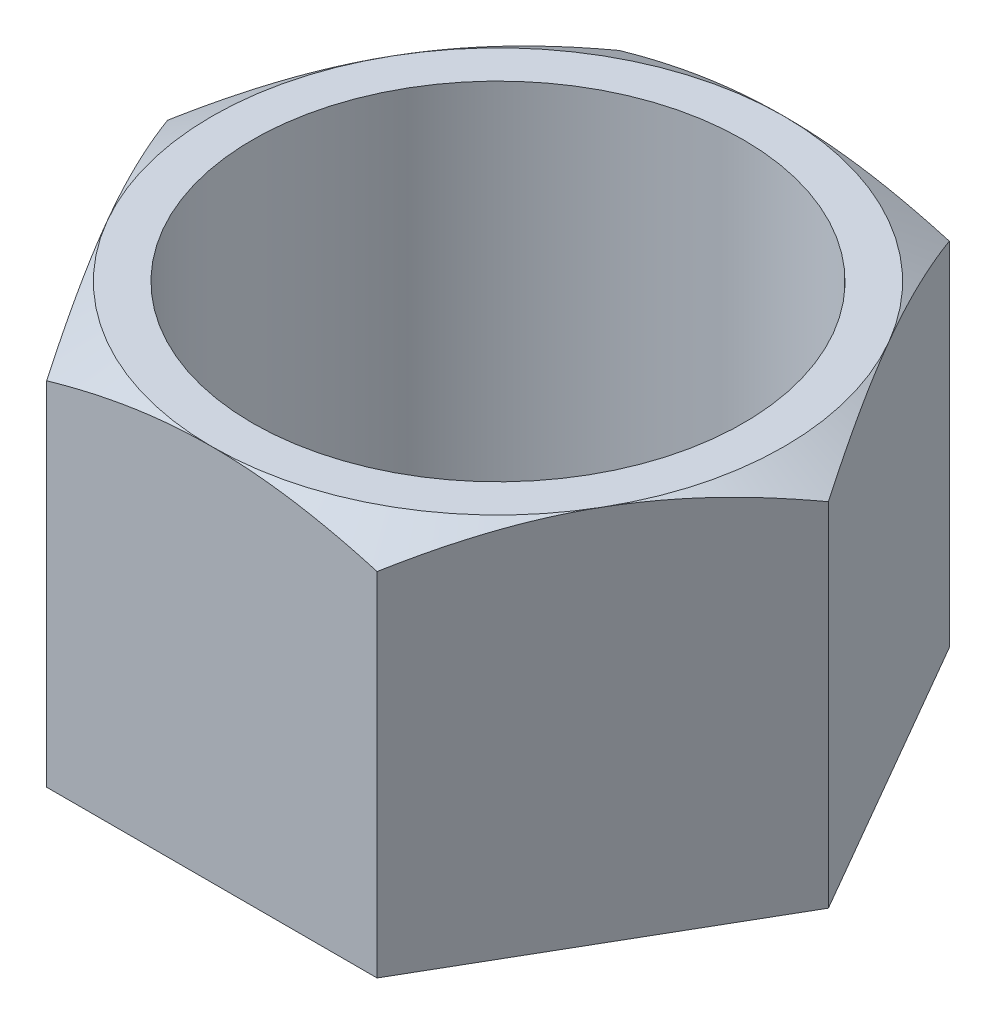
SolidWorks part; units mm, degrees
material "AISI 304"
ref_plane "Front Plane" through (0, 0, 0) normal (0, 0, 1) x (1, 0, 0)
ref_plane "Top Plane" through (0, 0, 0) normal (0, 1, 0) x (1, 0, 0)
ref_plane "Right Plane" through (0, 0, 0) normal (1, 0, 0) x (0, 0, -1)
sketch "Sketch1" plane through (0, 0, 0) normal (0, 1, 0) x (1, 0, 0)
  line L1 (17.5, 0) -> (8.75, 15.1554)
  line L2 (8.75, 15.1554) -> (-8.75, 15.1554)
  line L3 (-8.75, 15.1554) -> (-17.5, 0)
  line L4 (-17.5, 0) -> (-8.75, -15.1554)
  line L5 (-8.75, -15.1554) -> (8.75, -15.1554)
  line L6 (8.75, -15.1554) -> (17.5, 0)
  circle A0 centre (0, 0) radius 15.1554 construction
  dimension "D1" = 35
extrude "Boss-Extrude1" add sketch "Sketch1" along normal blind 20
sketch "Sketch2" plane through (0, 20, 0) normal (0, 1, 0) x (1, 0, 0)
  circle A0 centre (0, 0) radius 15.1554
extrude "Cut-Extrude1" cut sketch "Sketch2" against normal blind 20 draft 60 flip side to cut
sketch "Sketch3" plane through (0, 20, 0) normal (0, 1, 0) x (1, 0, 0)
  circle A0 centre (0, 0) radius 13
  dimension "D1" = 26
extrude "Cut-Extrude2" cut sketch "Sketch3" against normal through all
